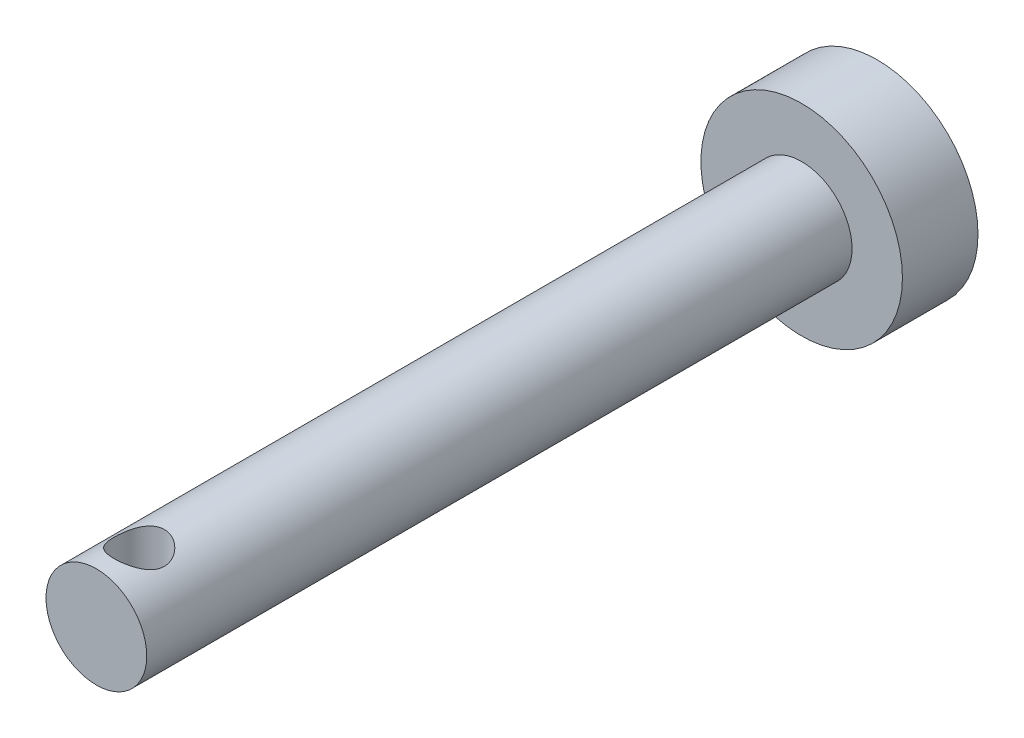
SolidWorks part; units mm, degrees
ref_plane "Front Plane" through (0, 0, 0) normal (0, 0, 1) x (1, 0, 0)
ref_plane "Top Plane" through (0, 0, 0) normal (0, 1, 0) x (1, 0, 0)
ref_plane "Right Plane" through (0, 0, 0) normal (1, 0, 0) x (0, 0, -1)
sketch "Sketch1" plane through (0, 0, 0) normal (1, 0, 0) x (0, 0, -1)
  line L0 (-125, 0) -> (125, 0) construction
  line L1 (125, 4) -> (125, -4) construction
  line L2 (125, 4) -> (122, 4) construction
  line L3 (-125, -2) -> (-125, 2) construction
  point P7 (-125, 0)
  dimension "Length" = 250
  dimension "Head Height" = 3
  dimension "Head Diameter" = 8
  dimension "Diameter" = 4
sketch "Sketch2" plane through (0, 0, 0) normal (1, 0, 0) x (0, 0, -1)
  line L0 (125, 0) -> (125, 4)
  line L1 (125, 4) -> (122, 4)
  line L2 (122, 4) -> (122, 2)
  line L3 (122, 2) -> (-125, 2)
  line L4 (-125, 2) -> (-125, 0)
  line L5 (-125, 0) -> (125, 0)
revolve "Revolve1" add sketch "Sketch2" angle 360 about L0
sketch "Sketch3" plane through (0, 0, 0) normal (1, 0, 0) x (0, 0, -1)
  line L0 (122, 4) -> (122, -4) construction
  line L1 (94, 4.0673) -> (-206, 4.0673)
  line L2 (94, 4.0673) -> (94, -3.766)
  line L3 (94, -3.766) -> (-206, -3.766)
  line L4 (-206, 4.0673) -> (-206, -3.766)
  line L5 (4.4, 0) -> (-4.4, 0) construction
  dimension "D1" = 7.8334
  dimension "D2" = 28
  dimension "D3" = 300
  dimension "D4" = 4.0673
extrude "Cut-Extrude1" cut sketch "Sketch3" against normal through all and the other way through all
sketch "Sketch4" plane through (0, 0, 0) normal (0, 1, 0) x (1, 0, 0)
  line L0 (-4, 122) -> (4, 122) construction
  line L1 (0, -4.4) -> (0, 4.4) construction
  circle A0 centre (0, 95.7) radius 1
  point P4 (0, 0)
  dimension "D1" = 2
  dimension "D2" = 26.3
extrude "Cut-Extrude2" cut sketch "Sketch4" against normal through all and the other way through all
